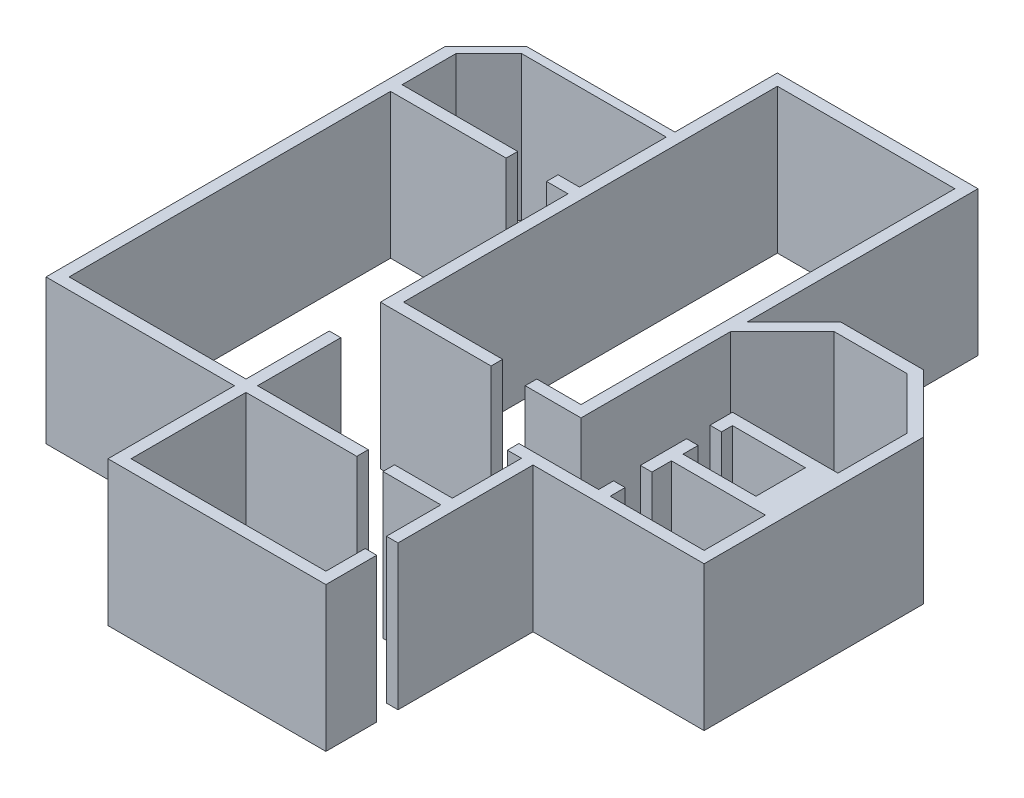
SolidWorks part; units mm, degrees
ref_plane "Front Plane" through (0, 0, 0) normal (0, 0, 1) x (1, 0, 0)
ref_plane "Top Plane" through (0, 0, 0) normal (0, 1, 0) x (1, 0, 0)
ref_plane "Right Plane" through (0, 0, 0) normal (1, 0, 0) x (0, 0, -1)
sketch "Sketch1" plane through (0, 0, 0) normal (0, 1, 0) x (1, 0, 0)
  line L0 (959.3738, 1394.5646) -> (959.3738, 2590)
  line L1 (-2090.6262, 2590) -> (-1197.3018, 3483.3243)
  line L2 (-1197.3018, 3483.3243) -> (66.0495, 3483.3243)
  line L3 (-2090.6262, 2590) -> (-2090.6262, 0)
  line L4 (-2090.6262, 0) -> (-3055.6676, 0)
  line L5 (-2290.6262, 200) -> (-2290.6262, 6667.5968)
  line L6 (-2290.6262, 6667.5968) -> (-5360.6262, 6667.5968)
  line L7 (-5560.6262, 3444.7098) -> (-5931.6689, 3444.7098)
  line L8 (-5931.6689, 3444.7098) -> (-5931.6689, 3244.7098)
  line L9 (-5560.6262, 4944.7098) -> (-5560.6262, 3444.7098)
  line L10 (-5931.6689, 3244.7098) -> (-5560.6262, 3244.7098)
  line L11 (-5560.6262, 4944.7098) -> (-8060.6262, 4944.7098)
  line L12 (-8630.6262, 4374.7098) -> (-8630.6262, 3444.7098)
  line L13 (-8630.6262, 3444.7098) -> (-6630.6262, 3444.7098)
  line L14 (-6630.6262, 3444.7098) -> (-6630.6262, 3244.7098)
  line L15 (-6630.6262, 3244.7098) -> (-8630.6262, 3244.7098)
  line L16 (-8630.6262, 3244.7098) -> (-8630.6262, -2315.2902)
  line L17 (-8630.6262, -2315.2902) -> (-5570.6262, -2315.2902)
  line L18 (-5570.6262, -2315.2902) -> (-5570.6262, -875.2902)
  line L19 (-5570.6262, -875.2902) -> (-5370.6262, -875.2902)
  line L20 (-5370.6262, -875.2902) -> (-5370.6262, -2315.2902)
  line L21 (-5370.6262, -2315.2902) -> (-3454.7164, -2315.2902)
  line L22 (959.3738, 1394.5646) -> (-865.7625, 1394.5646)
  line L23 (-865.7625, 1394.5646) -> (-865.7625, 1006.0257)
  line L24 (-8630.6262, 4374.7098) -> (-8060.6262, 4944.7098)
  line L25 (66.0495, 3483.3243) -> (959.3738, 2590)
  line L26 (-5560.6262, 3244.7098) -> (-5560.6262, 0)
  line L27 (-2000.6262, -1120.323) -> (-2244.5853, -1120.323)
  line L28 (-5360.6262, 200) -> (-5360.6262, 6667.5968)
  line L29 (-865.7625, 1006.0257) -> (-665.7625, 1006.0257)
  line L30 (-665.7625, 1006.0257) -> (-665.7625, 1194.5646)
  line L31 (-665.7625, 1194.5646) -> (596.1123, 1194.5646)
  line L32 (596.1123, 1194.5646) -> (596.1123, 339.1384)
  line L33 (596.1123, 339.1384) -> (-665.7625, 339.1384)
  line L34 (-665.7625, 339.1384) -> (-665.7625, 601.6881)
  line L35 (-665.7625, 601.6881) -> (-865.7625, 601.6881)
  line L36 (-865.7625, 601.6881) -> (-865.7625, -198.0812)
  line L37 (-865.7625, -198.0812) -> (-665.7625, -198.0812)
  line L38 (-665.7625, -198.0812) -> (-665.7625, 139.1384)
  line L39 (-665.7625, 139.1384) -> (959.3738, 139.1384)
  line L40 (959.3738, 139.1384) -> (959.3738, -920.323)
  line L41 (959.3738, -920.323) -> (-665.7625, -920.323)
  line L42 (-665.7625, -920.323) -> (-665.7625, -661.3525)
  line L43 (-665.7625, -661.3525) -> (-865.7625, -661.3525)
  line L44 (-865.7625, -661.3525) -> (-865.7625, -920.323)
  line L45 (-865.7625, -920.323) -> (-2244.5853, -920.323)
  line L46 (-2000.6262, -1120.323) -> (-2000.6262, -2315.2902)
  line L47 (-2000.6262, -2315.2902) -> (-3001.4682, -2315.2902)
  line L48 (-3001.4682, -2315.2902) -> (-3001.4682, -2515.2902)
  line L49 (-3001.4682, -2515.2902) -> (-2000.6262, -2515.2902)
  line L50 (-2000.6262, -2515.2902) -> (-2000.6262, -3455.8743)
  line L51 (-1800.6262, -3455.8743) -> (-2000.6262, -3455.8743)
  line L52 (1159.3738, -1120.323) -> (1159.3738, 2672.8427)
  line L53 (1159.3738, 2672.8427) -> (148.8922, 3683.3243)
  line L54 (148.8922, 3683.3243) -> (-1280.1446, 3683.3243)
  line L55 (-2000.6262, -3823.6829) -> (-1800.6262, -3823.6829)
  line L56 (-1800.6262, -3455.8743) -> (-1800.6262, -1120.323)
  line L57 (-1800.6262, -1120.323) -> (1159.3738, -1120.323)
  line L58 (-3454.7164, -2315.2902) -> (-3454.7164, -2515.2902)
  line L59 (-3454.7164, -2515.2902) -> (-5370.6262, -2515.2902)
  line L60 (-1800.6262, -3823.6829) -> (-1800.6262, -4703.4319)
  line L61 (-8830.6262, -2515.2902) -> (-8830.6262, 4386.8418)
  line L62 (-8830.6262, 4386.8418) -> (-8122.7582, 5094.7098)
  line L63 (-8122.7582, 5094.7098) -> (-5560.6262, 5094.7098)
  line L64 (-1800.6262, -4703.4319) -> (-5570.6262, -4703.4319)
  line L65 (-5570.6262, -4703.4319) -> (-5570.6262, -2515.2902)
  line L66 (-2000.6262, -3823.6829) -> (-2000.6262, -4503.4319)
  line L67 (-2000.6262, -4503.4319) -> (-5370.6262, -4503.4319)
  line L68 (-5370.6262, -4503.4319) -> (-5370.6262, -2515.2902)
  line L69 (-5570.6262, -2515.2902) -> (-8830.6262, -2515.2902)
  line L70 (-1280.1446, 3683.3243) -> (-2090.6262, 2872.8427)
  line L71 (-2090.6262, 2872.8427) -> (-2090.6262, 6867.5968)
  line L72 (-2090.6262, 6867.5968) -> (-5560.6262, 6867.5968)
  line L73 (-5560.6262, 6867.5968) -> (-5560.6262, 5094.7098)
  line L74 (-2290.6262, 200) -> (-3055.6676, 200)
  line L75 (-3055.6676, 200) -> (-3055.6676, 0)
  line L76 (-2244.5853, -1120.323) -> (-2244.5853, -920.323)
  line L77 (-5360.6262, 200) -> (-3647.0253, 200)
  line L78 (-3647.0253, 200) -> (-3647.0253, 0)
  line L79 (-3647.0253, 0) -> (-5560.6262, 0)
  dimension "D1" = 135
  dimension "D2" = 135
  dimension "D3" = 3050
  dimension "D5" = 200
  dimension "D7" = 3060
  dimension "D8" = 5560
  dimension "D9" = 200
  dimension "D10" = 1500
  dimension "D11" = 3070
  dimension "D12" = 3070
  dimension "D13" = 150
  dimension "D15" = 2000
  dimension "D16" = 135
  dimension "D17" = 2500
  dimension "D18" = 2590
  dimension "D19" = 1440
  dimension "D20" = 1500
  dimension "D21" = 200
  dimension "D22" = 3370
  dimension "D23" = 200
  dimension "D24" = 200
  dimension "D25" = 200
  dimension "D26" = 150
  dimension "D27" = 200
  dimension "D28" = 200
  dimension "D29" = 200
  dimension "D30" = 200
  dimension "D31" = 200
  dimension "D32" = 200
  dimension "D33" = 200
  dimension "D34" = 200
  dimension "D35" = 200
extrude "Boss-Extrude1" add sketch "Sketch1" along normal blind 2500
equation "\"WIDTH_WALL\"=200"
equation "\"D4@Sketch1\"=\"WIDTH_WALL\""
equation "\"D5@Sketch1\"=\"WIDTH_WALL\""
equation "\"D6@Sketch1\"=\"WIDTH_WALL\""
equation "\"D21@Sketch1\"=\"WIDTH_WALL\""
equation "\"D23@Sketch1\"=\"WIDTH_WALL\""
equation "\"D24@Sketch1\"=\"WIDTH_WALL\""
equation "\"D25@Sketch1\"=\"WIDTH_WALL\""
equation "\"D27@Sketch1\" = \"WIDTH_WALL\""
equation "\"D28@Sketch1\"=\"WIDTH_WALL\""
equation "\"D29@Sketch1\"=\"WIDTH_WALL\""
equation "\"D30@Sketch1\"=\"WIDTH_WALL\""
equation "\"D31@Sketch1\"=\"WIDTH_WALL\""
equation "\"D32@Sketch1\"=\"WIDTH_WALL\""
equation "\"D33@Sketch1\"=\"WIDTH_WALL\""
equation "\"D9@Sketch1\"=\"WIDTH_WALL\""
equation "\"D34@Sketch1\"=\"WIDTH_WALL\""
equation "\"D35@Sketch1\"=\"WIDTH_WALL\""
